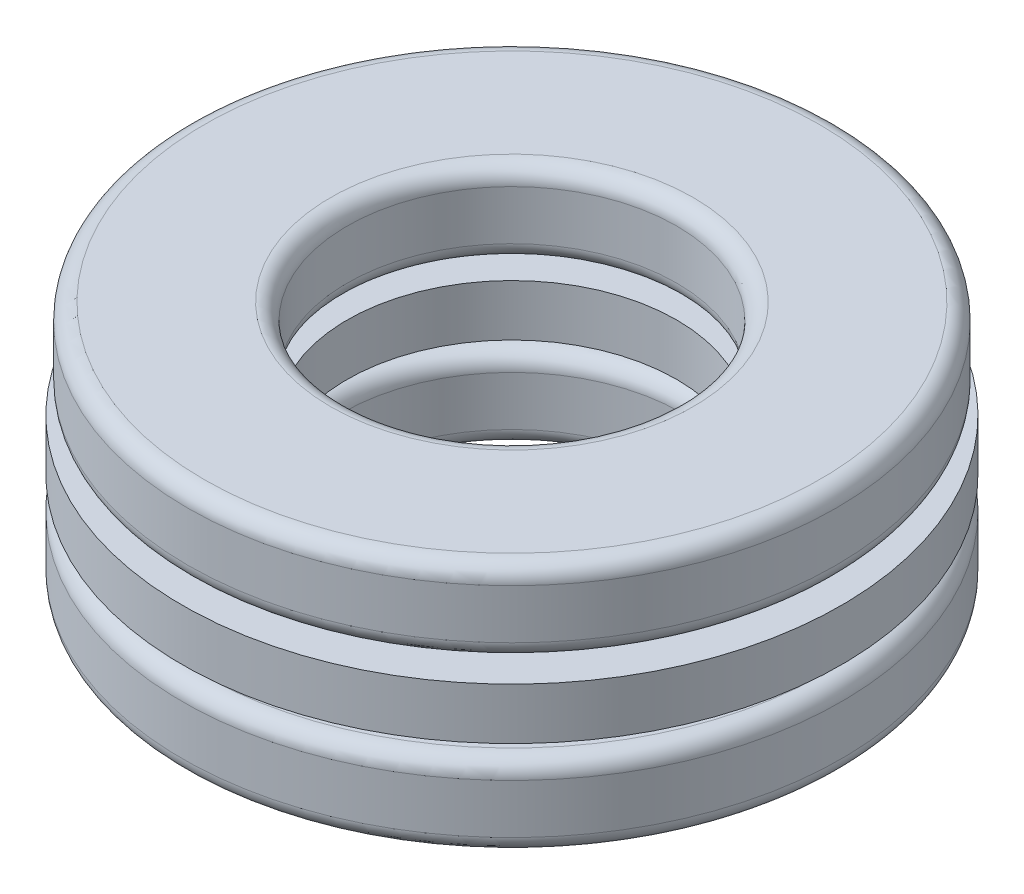
SolidWorks part; units mm, degrees
material "Alloy Steel"
ref_plane "Front Plane" through (0, 0, 0) normal (0, 0, 1) x (1, 0, 0)
ref_plane "Top Plane" through (0, 0, 0) normal (0, 1, 0) x (1, 0, 0)
ref_plane "Right Plane" through (0, 0, 0) normal (1, 0, 0) x (0, 0, -1)
sketch "Sketch1" plane through (0, 0, 0) normal (1, 0, 0) x (0, 0, -1)
  line L0 (-6, 0) -> (6, 0) construction
  line L1 (0, -2.25) -> (0, 2.25) construction
  line L2 (-6, 0.4687) -> (-3, 0.4687)
  line L3 (-6, 0.4687) -> (-6, -0.4688)
  line L4 (-6, -0.4688) -> (-3, -0.4688)
  line L5 (-3, 0.4687) -> (-3, -0.4688)
  line L6 (-4.5, 0.75) -> (-4.5, -0.75) construction
  line L7 (-4.5, 0.75) -> (-4.5, 2.25) construction
  circle A0 centre (-4.5, 0) radius 0.75 construction
  point P13 (-4.5, 0.4688)
  dimension "D1" = 1.5
  dimension "OD" = 12
  dimension "Shaft Dia" = 6
  dimension "Th" = 4.5
  dimension "D2" = 0.9375
  dimension "D3" = 1.5
revolve "Revolve1" add sketch "Sketch1" angle 360 about L1
sketch "Sketch3" plane through (0, 0, 0) normal (1, 0, 0) x (0, 0, -1)
  line L0 (-4.5, 0.75) -> (-4.5, -0.75)
  arc A0 (-4.5, 0.75) -> (-4.5, -0.75) centre (-4.5, 0) ccw
  circle A1 centre (-4.5, 0) radius 0.75 construction
revolve "Cut-Revolve1" cut sketch "Sketch3" angle 360 about L0
sketch "Sketch2" plane through (0, 0, 0) normal (1, 0, 0) x (0, 0, -1)
  line L0 (-4.5, 0.75) -> (-4.5, -0.75)
  arc A0 (-4.5, 0.75) -> (-4.5, -0.75) centre (-4.5, 0) ccw
  circle A2 centre (-4.5, 0) radius 0.75 construction
revolve "Revolve2" add sketch "Sketch2" angle 360 about L0
ref_axis "Axis1" through (0, 2.25, 0) along (0, -1, 0)
pattern_circular "CirPattern1" count 5 every 72 about axis through (0, 2.25, 0) along (0, -1, 0) of bodies 187
pattern_circular "CirPattern2" count 5 every 72 about axis through (0, 0, 0) along (0, 1, 0) of "Cut-Revolve1"
sketch "Sketch4" plane through (0, 0, 0) normal (1, 0, 0) x (0, 0, -1)
  line L0 (-6, 0.4687) -> (-6, -0.4688) construction
  line L2 (-6, 2.25) -> (-6, -2.25) construction
  line L3 (-5.6, 2.25) -> (-3.3, 2.25)
  line L4 (-3, 1.05) -> (-3, 1.95)
  line L5 (-5.7, -2.25) -> (-3.4, -2.25)
  line L6 (-6, -1.95) -> (-6, -1.05)
  line L8 (-5.6, 0.75) -> (-3.3, 0.75)
  line L10 (-3, 0.4687) -> (-3, -0.4688) construction
  line L11 (0, 0) -> (-6, 0) construction
  line L12 (-6, 0) -> (6, 0) construction
  line L13 (0, 0) -> (0, 2.25) construction
  line L14 (-5.9, 1.95) -> (-5.9, 1.05)
  line L15 (-3.1, -1.05) -> (-3.1, -1.95)
  line L16 (-5.7, -0.75) -> (-3.4, -0.75)
  arc A0 (-5.6, 2.25) -> (-5.9, 1.95) centre (-5.6, 1.95) ccw
  arc A1 (-3.3, 2.25) -> (-3, 1.95) centre (-3.3, 1.95) cw
  arc A2 (-3.3, 0.75) -> (-3, 1.05) centre (-3.3, 1.05) ccw
  arc A3 (-3.4, -0.75) -> (-3.1, -1.05) centre (-3.4, -1.05) cw
  arc A4 (-6, -1.05) -> (-5.7, -0.75) centre (-5.7, -1.05) cw
  arc A5 (-5.7, -2.25) -> (-6, -1.95) centre (-5.7, -1.95) cw
  arc A6 (-5.6, 0.75) -> (-5.9, 1.05) centre (-5.6, 1.05) cw
  arc A7 (-3.4, -2.25) -> (-3.1, -1.95) centre (-3.4, -1.95) ccw
  point P25 (-6, -0.75)
  point P26 (-8.5, 0.0333)
  point P29 (-8.5, -0.0333)
  dimension "r" = 0.3
  dimension "D5" = 12
  dimension "D1" = 1.5
  dimension "Ht" = 4.5
  dimension "D3" = 6
  dimension "dia2" = 6.2
  dimension "dia1" = 11.8
revolve "Revolve3" add sketch "Sketch4" angle 360 about L1
equation "\"D1@Sketch1\" = \"Th@Sketch1\"/3"
equation "\"D2@Sketch1\" = \"D1@Sketch1\"*.625"
equation "\"Balls@CirPattern1\" = \"OD@Sketch1\"*.375"
equation "\"Angle@CirPattern1\" = 360/\"Balls@CirPattern1\""
equation "\"D1@CirPattern2\" = \"Balls@CirPattern1\""
equation "\"D2@CirPattern2\" = \"Angle@CirPattern1\""
equation "\"D1@Sketch4\" = \"D3@Sketch1\""
